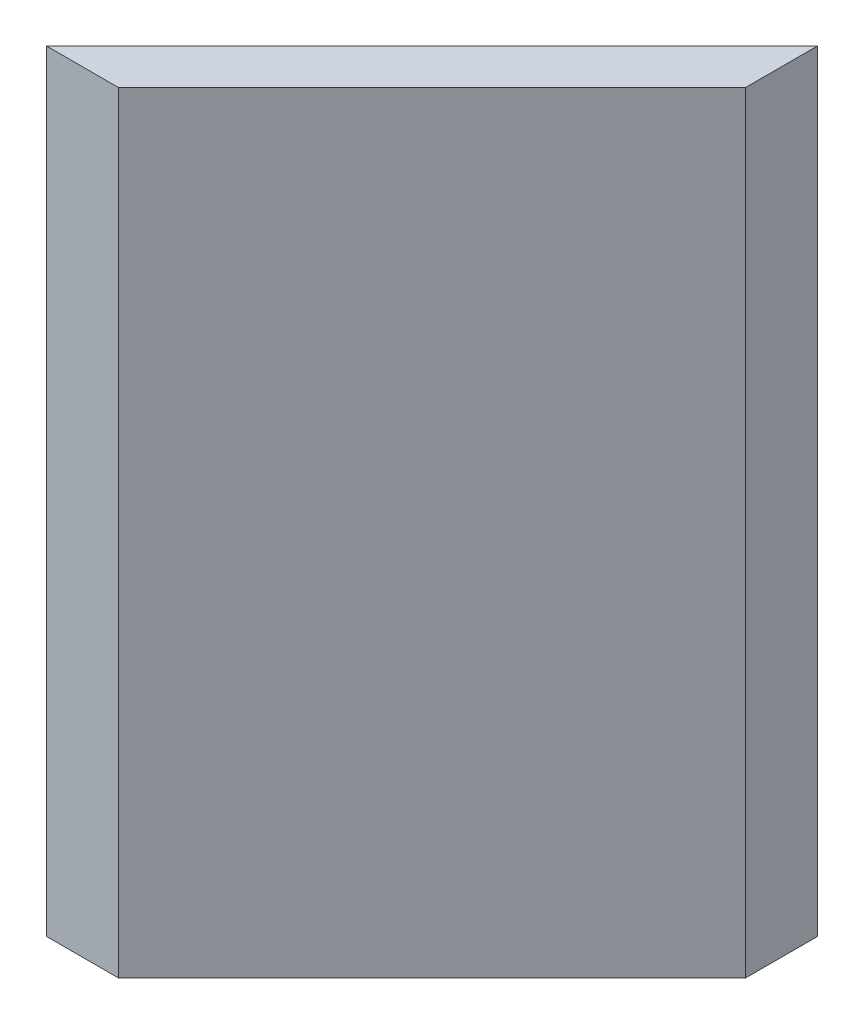
SolidWorks part; units mm, degrees
ref_plane "Front Plane" through (0, 0, 0) normal (0, 0, 1) x (1, 0, 0)
ref_plane "Top Plane" through (0, 0, 0) normal (0, 1, 0) x (1, 0, 0)
ref_plane "Right Plane" through (0, 0, 0) normal (1, 0, 0) x (0, 0, -1)
sketch "Sketch1" plane through (0, 0, 0) normal (0, 1, 0) x (1, 0, 0)
  line L0 (0, 0) -> (0, 90.5977) construction
  line L1 (0, 0) -> (-112.5687, 0) construction
  line L2 (-74, 0) -> (0, 74)
  line L3 (0, 74) -> (0, 90.9706)
  line L4 (0, 90.9706) -> (-90.9706, 0)
  line L5 (-90.9706, 0) -> (-74, 0)
  dimension "D1" = 74
  dimension "D2" = 12
extrude "Boss-Extrude1" add sketch "Sketch1" along normal blind 182
